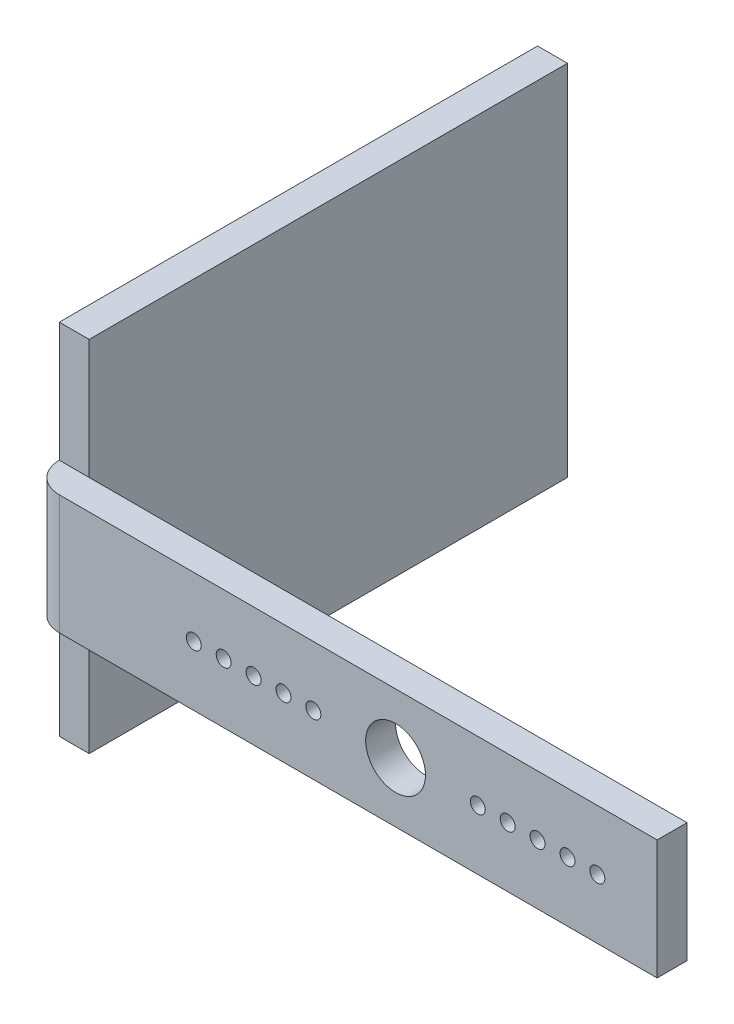
SolidWorks part; units mm, degrees
ref_plane "Front Plane" through (0, 0, 0) normal (0, 0, 1) x (1, 0, 0)
ref_plane "Top Plane" through (0, 0, 0) normal (0, 1, 0) x (1, 0, 0)
ref_plane "Right Plane" through (0, 0, 0) normal (1, 0, 0) x (0, 0, -1)
sketch "Sketch1" plane through (0, 0, 0) normal (0, 0, 1) x (1, 0, 0)
  line L1 (-31.75, -6.35) -> (31.75, -6.35)
  line L2 (-31.75, -6.35) -> (-31.75, 6.35)
  line L3 (-31.75, 6.35) -> (31.75, 6.35)
  line L4 (31.75, -6.35) -> (31.75, 6.35)
  line L5 (-31.75, -6.35) -> (31.75, 6.35) construction
  line L6 (-31.75, 6.35) -> (31.75, -6.35) construction
  point P0 (0, 0)
  dimension "D1" = 12.7
  dimension "D2" = 63.5
extrude "Boss-Extrude1" add sketch "Sketch1" along normal blind 3.175
sketch "Sketch2" plane through (-31.75, 0, 0) normal (-1, 0, 0) x (0, 0, 1)
  line L1 (-50.8, 19.05) -> (0, 19.05)
  line L2 (-50.8, 19.05) -> (-50.8, -19.05)
  line L3 (-50.8, -19.05) -> (0, -19.05)
  line L4 (0, 19.05) -> (0, -19.05)
  line L7 (1.5875, 6.35) -> (1.5875, -6.35) construction
  line L8 (3.175, 6.35) -> (0, 6.35) construction
  line L9 (3.175, -6.35) -> (0, -6.35) construction
  line L10 (0, 0) -> (3.175, 0) construction
  line L11 (0, 6.35) -> (0, -6.35) construction
  line L12 (3.175, 6.35) -> (3.175, -6.35) construction
  dimension "D1" = 19.05
  dimension "D2" = 50.8
  dimension "D3" = 0
  dimension "D4" = 19.05
extrude "Boss-Extrude2" add sketch "Sketch2" along normal blind 3.175
sketch "Sketch3" plane through (0, 0, 3.175) normal (0, 0, 1) x (1, 0, 0)
  line L0 (31.75, -6.35) -> (31.75, 6.35) construction
  circle A0 centre (25.4, 0) radius 0.7937
  dimension "D1" = 1.5875
  dimension "D2" = 6.35
sketch "Sketch4" plane through (0, 6.35, 0) normal (0, 1, 0) x (1, 0, 0)
  line L0 (-34.925, 0) -> (-31.75, 0)
  line L1 (-31.75, 0) -> (-31.75, -3.175)
  arc A0 (-31.75, -3.175) -> (-34.925, 0) centre (-31.75, 0) cw
extrude "Boss-Extrude3" add sketch "Sketch4" against normal blind 12.7
extrude "Cut-Extrude1" cut sketch "Sketch3" against normal blind 6.35
pattern_linear "LPattern1" count 5 spacing 3.175 along (-1, 0, 0) of "Cut-Extrude1"
sketch "Sketch5" plane through (0, 0, 3.175) normal (0, 0, 1) x (1, 0, 0)
  line L0 (11.9062, 0) -> (-3.9688, 0) construction
  circle A0 centre (12.7, 0) radius 0.7937 construction
  circle A1 centre (-4.7625, 0) radius 0.7938
  dimension "D2" = 1.5875
  dimension "D3" = 0.7937
  dimension "D1" = 15.875
extrude "Cut-Extrude2" cut sketch "Sketch5" against normal blind 6.35
pattern_linear "LPattern2" count 5 spacing 3.175 along (-1, 0, 0) of "Cut-Extrude2"
sketch "Sketch6" plane through (0, 0, 3.175) normal (0, 0, 1) x (1, 0, 0)
  line L0 (-4.7625, 0) -> (12.7, 0) construction
  circle A0 centre (3.9687, 0) radius 3.175
  dimension "D1" = 6.35
extrude "Cut-Extrude3" cut sketch "Sketch6" against normal through all
